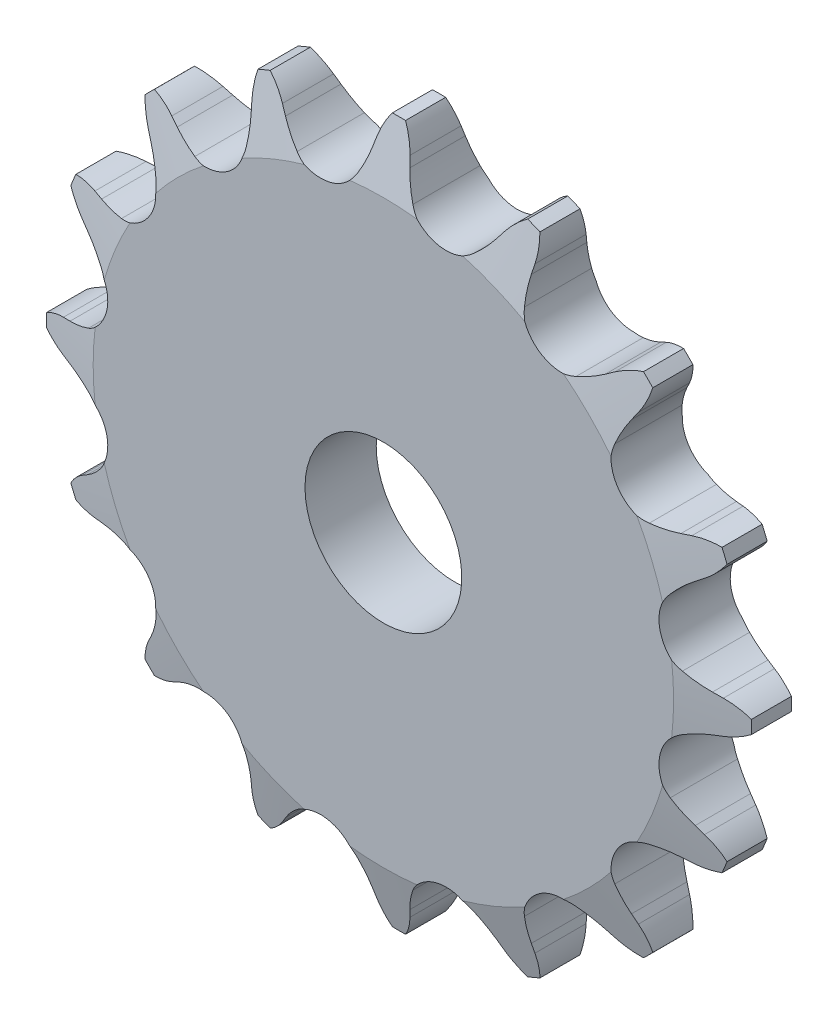
SolidWorks part; units mm, degrees
ref_plane "Front Plane" through (0, 0, 0) normal (0, 0, 1) x (1, 0, 0)
ref_plane "Top Plane" through (0, 0, 0) normal (0, 1, 0) x (1, 0, 0)
ref_plane "Right Plane" through (0, 0, 0) normal (1, 0, 0) x (0, 0, -1)
sketch "Sketch0" plane through (0, 0, 0) normal (0, 0, 1) x (1, 0, 0)
  line L0 (6.35, -31.9236) -> (0, 0) construction
  line L1 (0, 0) -> (18.0833, -27.0635) construction
  line L2 (0, 0) -> (-6.35, -31.9236) construction
  line L3 (6.35, -31.9236) -> (18.0833, -27.0635) construction
  line L4 (6.35, -31.9236) -> (-6.35, -31.9236) construction
  line L5 (11.2367, -31.5036) -> (10.7092, -30.764)
  line L6 (6.35, -31.9236) -> (0, -33.1867) construction
  line L7 (1.6745, -33.4056) -> (1.8789, -32.5205)
  line L8 (0, -31.9236) -> (0, -35.7336) construction
  line L9 (8.9342, -28.8439) -> (2.2748, -36.7802) construction
  line L10 (0, 0) -> (0, -31.9236) construction
  line L11 (10.7092, -30.764) -> (2.2748, -36.7802) construction
  line L12 (0, -35.7336) -> (0, -36.4943) construction
  line L13 (16.6002, -27.6778) -> (11.2367, -31.5036) construction
  circle A0 centre (0, 0) radius 35.7336 construction
  circle A1 centre (0, 0) radius 32.549 construction
  arc A2 (-5.7133, -38.4401) -> (19.9888, -33.3277) centre (0, 0) ccw
  circle A3 centre (0, 0) radius 36.4943 construction
  circle A4 centre (6.35, -31.9236) radius 3.9624 construction
  arc A7 (8.9342, -28.8439) -> (2.7839, -30.0672) centre (6.35, -31.9236) ccw
  circle A8 centre (6.35, -31.9236) radius 4.0203 construction
  arc A9 (11.2367, -31.5036) -> (19.9888, -33.3277) centre (16.6002, -27.6778) ccw
  arc A10 (10.7092, -30.764) -> (8.9342, -28.8439) centre (2.2748, -36.7802) ccw
  arc A11 (1.6745, -33.4056) -> (-5.7133, -38.4401) centre (-4.7447, -31.9236) cw
  arc A12 (1.8789, -32.5205) -> (2.7839, -30.0672) centre (11.9735, -34.851) cw
  dimension "D1" = 4.0203
  dimension "Dr" = 7.9248
  dimension "Ds" = 8.0406
  dimension "R" = 4.0203
  dimension "Pitch" = 12.7
  dimension "A" = 38.75
  dimension "360/N" = 22.5
  dimension "B" = 14.5
  dimension "ab" = 11.0947
  dimension "J" = 3.81
  dimension "ac" = 6.3398
sketch "Sketch1" plane through (0, 0, 0) normal (1, 0, 0) x (0, 0, -1)
  line L0 (3.6068, 0) -> (-3.6068, 0)
  line L1 (-3.6068, 0) -> (-3.6068, 29.3836)
  line L2 (-3.6068, 29.3836) -> (-2.0193, 35.7336)
  line L3 (-2.0193, 35.7336) -> (2.0193, 35.7336)
  line L4 (2.0193, 35.7336) -> (3.6068, 29.3836)
  line L5 (3.6068, 29.3836) -> (3.6068, 0)
  line L7 (0, 35.7336) -> (0, 0) construction
  line L8 (-3.6068, 29.3836) -> (3.6068, 29.3836) construction
  line L9 (0, 35.7336) -> (0, -35.7336) construction
  line L10 (-3.6068, 29.3836) -> (-3.6068, 35.7336) construction
  line L11 (-3.6068, 35.7336) -> (-2.0193, 35.7336) construction
  line L12 (2.0193, 35.7336) -> (3.6068, 35.7336) construction
  line L13 (3.6068, 35.7336) -> (3.6068, 29.3836) construction
  dimension "t" = 7.2136
  dimension "g" = 1.5875
  dimension "h" = 6.35
revolve "Revolve1" add sketch "Sketch1" angle 360 mid plane about L0
extrude "Cut-Extrude1" cut sketch "Sketch0" against normal through all and the other way through all
pattern_circular "CirPattern1" count 16 over 360 about axis through (0, 0, 0) along (0, 0, 1) of "Cut-Extrude1"
sketch "Sketch2" plane through (0, 0, 0) normal (0, 0, 1) x (1, 0, 0)
  circle A0 centre (0, 0) radius 7.9375 construction
  circle A1 centre (0, 0) radius 30.1625
  circle A2 centre (0, 0) radius 35.687 construction
  dimension "Bore" = 15.875
  dimension "Hub Dia." = 60.325
  dimension "OD" = 71.374
sketch "Sketch3" plane through (0, 0, 0) normal (0, 0, 1) x (1, 0, 0)
  circle A0 centre (0, 0) radius 7.9375 construction
  circle A1 centre (0, 0) radius 7.9375
  circle A2 centre (0, 0) radius 35.687 construction
  circle A3 centre (0, 0) radius 35.687
extrude "Cut-Extrude2" cut sketch "Sketch3" along normal through all and the other way through all flip side to cut
equation "\"360/N@Sketch0\" = 360/\"Teeth@CirPattern1\""
equation "\"Ds@Sketch0\" = 1.005 * \"Dr@Sketch0\" + 0.003"
equation "\"R@Sketch0\" = 1/2 * \"Ds@Sketch0\""
equation "\"A@Sketch0\" = 35 +  ( 60 / \"Teeth@CirPattern1\" ) "
equation "\"B@Sketch0\" = 18 -  ( 56 / \"Teeth@CirPattern1\" )"
equation "\"ac@Sketch0\" = 0.8 * \"Dr@Sketch0\""
equation "\"ab@Sketch0\" = 1.4 * \"Dr@Sketch0\""
equation "\"J@Sketch0\" = 0.3 * \"Pitch@Sketch0\""
equation "\"h@Sketch1\" = \"Pitch@Sketch0\" / 2"
equation "\"g@Sketch1\" = \"h@Sketch1\" / 4"
